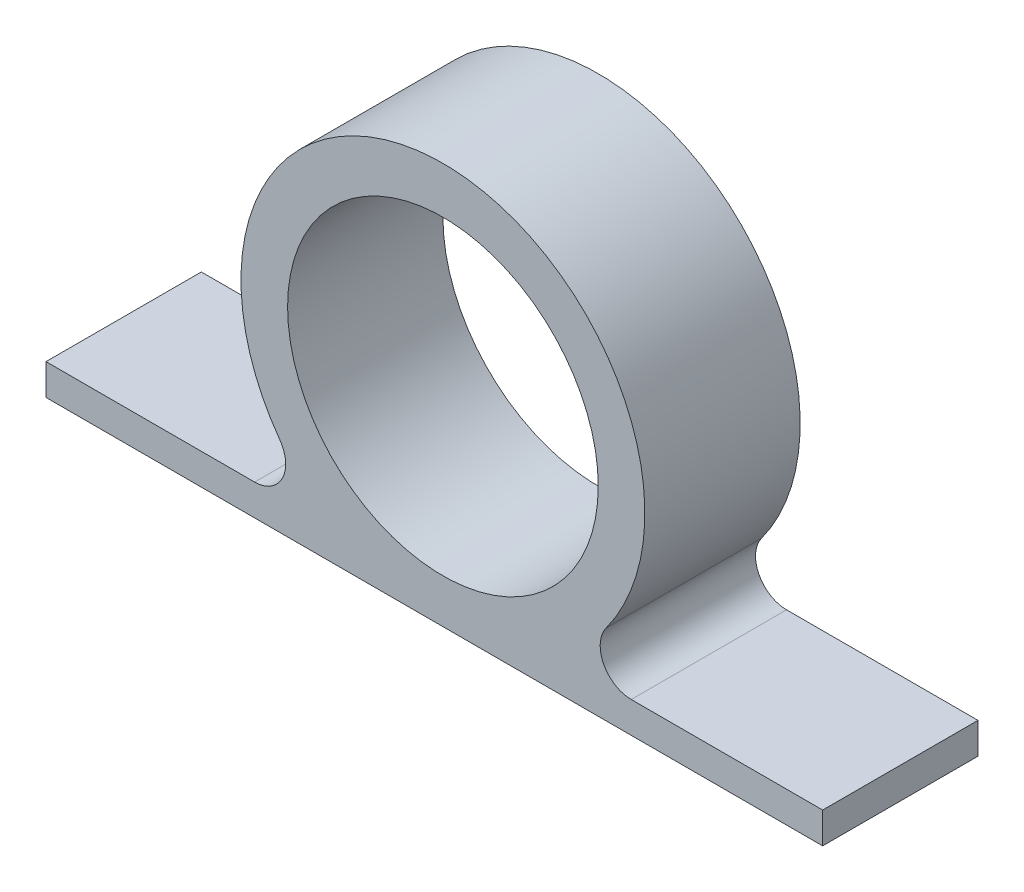
SolidWorks part; units mm, degrees
ref_plane "Plan de face" through (0, 0, 0) normal (0, 0, 1) x (1, 0, 0)
ref_plane "Plan de dessus" through (0, 0, 0) normal (0, 1, 0) x (1, 0, 0)
ref_plane "Plan de droite" through (0, 0, 0) normal (1, 0, 0) x (0, 0, -1)
sketch "Esquisse1" plane through (0, 0, 0) normal (0, 0, 1) x (1, 0, 0)
  line L0 (0, -12.8333) -> (-25.5528, -12.8333)
  line L1 (0, -12.8333) -> (24.4472, -12.8333)
  line L2 (-25.5528, -12.8333) -> (-25.5528, -10.8333)
  line L3 (-25.5528, -10.8333) -> (-12.1232, -10.8333)
  line L4 (24.4472, -12.8333) -> (24.4472, -10.8333)
  line L5 (24.4472, -10.8333) -> (12.1232, -10.8333)
  circle A0 centre (0, 0) radius 10
  arc A1 (10.5068, -7.6556) -> (-10.5068, -7.6556) centre (0, 0) ccw
  arc A2 (12.1232, -10.8333) -> (10.5068, -7.6556) centre (12.1232, -8.8333) cw
  arc A3 (-12.1232, -10.8333) -> (-10.5068, -7.6556) centre (-12.1232, -8.8333) ccw
  point P14 (-7.186, -10.8333)
  dimension "D1" = 2
  dimension "D2" = 2
  dimension "D3" = 13
extrude "Boss.-Extru.3" add sketch "Esquisse1" along normal blind 10
